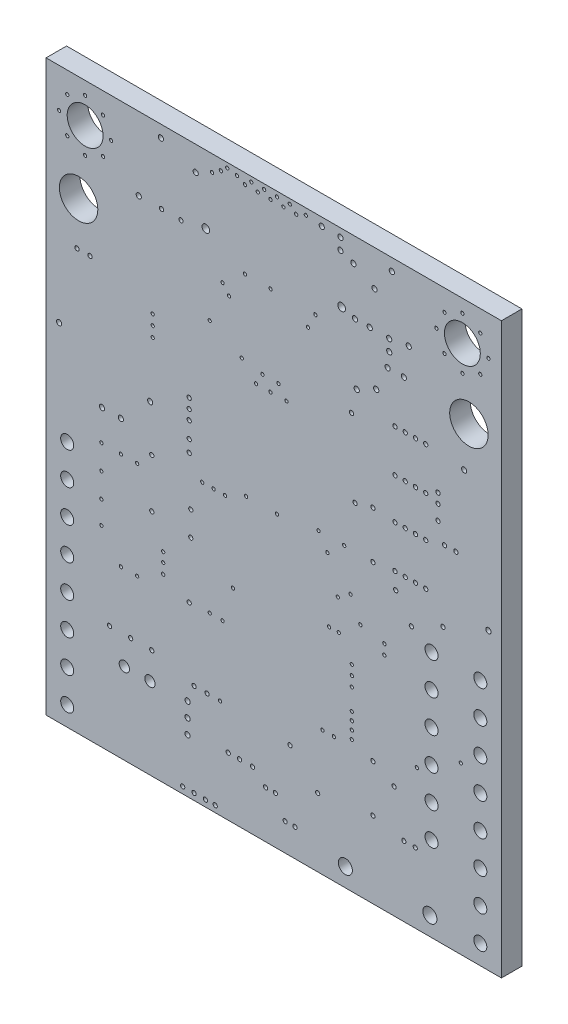
SolidWorks part; units mm, degrees
ref_plane "Спереди" through (0, 0, 0) normal (0, 0, 1) x (1, 0, 0)
ref_plane "Сверху" through (0, 0, 0) normal (0, 1, 0) x (1, 0, 0)
ref_plane "Справа" through (0, 0, 0) normal (1, 0, 0) x (0, 0, -1)
ref_plane "Dielectric_Layer Layer 1" through (0, 0, 1.6) normal (0, 0, 1) x (1, 0, 0)
sketch "Sketch1" plane through (0, 0, 0) normal (0, 0, 1) x (1, 0, 0)
  line L0 (0, 44.45) -> (0, 0)
  line L1 (0, 0) -> (35.56, 0)
  line L2 (35.56, 0) -> (35.56, 44.45)
  line L3 (35.56, 44.45) -> (0, 44.45)
extrude "Board_Outline" add sketch "Sketch1" along normal blind 1.6 separate body
sketch "Sketch2" plane through (0, 0, 0) normal (0, 0, 1) x (1, 0, 0)
  circle A0 centre (23.08, 39.14) radius 0.3
  circle A1 centre (12.48, 39.14) radius 0.3
  circle A2 centre (32.385, 12.954) radius 0.127
  circle A3 centre (15.621, 22.606) radius 0.127
  circle A4 centre (28.848, 23.368) radius 0.1651
  circle A5 centre (13.589, 7.747) radius 0.127
  circle A6 centre (19.53, 43.6372) radius 0.127
  circle A7 centre (24.543, 18.383) radius 0.127
  circle A8 centre (16.395, 30.607) radius 0.127
  circle A9 centre (22.098, 17.018) radius 0.127
  circle A10 centre (16.895, 31.496) radius 0.127
  circle A11 centre (22.86, 17.018) radius 0.127
  circle A12 centre (12.78, 33.067) radius 0.127
  circle A13 centre (15.53, 43.6372) radius 0.127
  circle A14 centre (12.192, 21.844) radius 0.127
  circle A15 centre (16.03, 44.069) radius 0.127
  circle A16 centre (13.081, 21.844) radius 0.127
  circle A17 centre (16.53, 43.6372) radius 0.127
  circle A18 centre (13.97, 21.844) radius 0.127
  circle A19 centre (17.03, 44.069) radius 0.127
  circle A20 centre (18.149, 31.496) radius 0.127
  circle A21 centre (18.03, 44.069) radius 0.127
  circle A22 centre (12.78, 13.288) radius 0.127
  circle A23 centre (19.03, 44.069) radius 0.127
  circle A24 centre (13.78, 13.272) radius 0.127
  circle A25 centre (17.526, 30.607) radius 0.127
  circle A26 centre (18.034, 22.606) radius 0.127
  circle A27 centre (18.776, 30.627) radius 0.127
  circle A28 centre (22.781, 19.383) radius 0.127
  circle A29 centre (15.28, 31.79) radius 0.127
  circle A30 centre (18.53, 43.6372) radius 0.127
  circle A31 centre (4.318, 20.574) radius 0.127
  circle A32 centre (4.318, 16.764) radius 0.127
  circle A33 centre (8.255, 21.717) radius 0.1651
  circle A34 centre (5.842, 20.574) radius 0.127
  circle A35 centre (7.112, 12.954) radius 0.127
  circle A36 centre (30.988, 21.463) radius 0.1651
  circle A37 centre (27.305, 22.098) radius 0.1651
  circle A38 centre (4.318, 18.669) radius 0.127
  circle A39 centre (4.318, 14.986) radius 0.127
  circle A40 centre (30.607, 30.353) radius 0.1651
  circle A41 centre (28.829, 5.461) radius 0.1651
  circle A42 centre (27.94, 5.461) radius 0.1651
  circle A43 centre (5.842, 12.954) radius 0.127
  circle A44 centre (11.303, 17.653) radius 0.1651
  circle A45 centre (7.112, 20.574) radius 0.127
  circle A46 centre (11.176, 26.289) radius 0.1651
  circle A47 centre (11.176, 27.051) radius 0.1651
  circle A48 centre (6.604, 8.509) radius 0.1651
  circle A49 centre (8.255, 8.509) radius 0.1651
  circle A50 centre (19.05, 7.493) radius 0.1651
  circle A51 centre (1.016, 27.051) radius 0.2032
  circle A52 centre (4.3688, 22.987) radius 0.2032
  circle A53 centre (25.527, 26.797) radius 0.1651
  circle A54 centre (25.527, 5.969) radius 0.1651
  circle A55 centre (30.607, 29.591) radius 0.1651
  circle A56 centre (11.176, 13.208) radius 0.1651
  circle A57 centre (11.176, 25.527) radius 0.1651
  circle A58 centre (15.113, 4.572) radius 0.1651
  circle A59 centre (14.224, 4.572) radius 0.1651
  circle A60 centre (16.129, 4.572) radius 0.1651
  circle A61 centre (11.557, 7.747) radius 0.1651
  circle A62 centre (24.13, 26.416) radius 0.1651
  circle A63 centre (34.544, 22.987) radius 0.2032
  circle A64 centre (28.525, 20.27) radius 0.1651
  circle A65 centre (28.848, 26.67) radius 0.1651
  circle A66 centre (32.648, 32.902) radius 0.2032
  circle A67 centre (23.85, 32.359) radius 0.1651
  circle A68 centre (17.907, 3.683) radius 0.1651
  circle A69 centre (17.145, 3.683) radius 0.1651
  circle A70 centre (11.049, 5.334) radius 0.2032
  circle A71 centre (25.781, 34.925) radius 0.2032
  circle A72 centre (27.94, 36.83) radius 0.2032
  circle A73 centre (26.67, 36.83) radius 0.2032
  circle A74 centre (25.654, 41.656) radius 0.2032
  circle A75 centre (24.257, 34.163) radius 0.2032
  circle A76 centre (17.53, 37.592) radius 0.127
  circle A77 centre (15.53, 37.592) radius 0.127
  circle A78 centre (21.03, 37.592) radius 0.127
  circle A79 centre (11.049, 4.191) radius 0.2032
  circle A80 centre (11.049, 6.477) radius 0.2032
  circle A81 centre (14.28, 35.489) radius 0.127
  circle A82 centre (14.149, 44.069) radius 0.127
  circle A83 centre (13.78, 36.132) radius 0.127
  circle A84 centre (13.649, 43.6372) radius 0.127
  circle A85 centre (21.59, 9.779) radius 0.127
  circle A86 centre (22.479, 9.779) radius 0.127
  circle A87 centre (9.144, 14.097) radius 0.127
  circle A88 centre (8.325, 29.699) radius 0.127
  circle A89 centre (8.325, 30.499) radius 0.127
  circle A90 centre (9.144, 14.883) radius 0.127
  circle A91 centre (9.144, 15.621) radius 0.127
  circle A92 centre (8.325, 31.299) radius 0.127
  circle A93 centre (3.048, 43.434) radius 0.127
  circle A94 centre (5.08, 41.402) radius 0.127
  circle A95 centre (5.842, 22.987) radius 0.2032
  circle A96 centre (7.239, 38.735) radius 0.2032
  circle A97 centre (1.016, 41.402) radius 0.127
  circle A98 centre (3.048, 39.37) radius 0.127
  circle A99 centre (8.966, 43.51) radius 0.2032
  circle A100 centre (27, 43.51) radius 0.2032
  circle A101 centre (24.003, 42.545) radius 0.2032
  circle A102 centre (11.684, 42.545) radius 0.2032
  circle A103 centre (4.445, 42.799) radius 0.127
  circle A104 centre (1.651, 42.799) radius 0.127
  circle A105 centre (1.651, 40.005) radius 0.127
  circle A106 centre (4.445, 40.005) radius 0.127
  circle A107 centre (32.512, 43.434) radius 0.127
  circle A108 centre (30.48, 41.402) radius 0.127
  circle A109 centre (34.544, 41.402) radius 0.127
  circle A110 centre (32.512, 39.37) radius 0.127
  circle A111 centre (31.115, 42.799) radius 0.127
  circle A112 centre (31.115, 40.005) radius 0.127
  circle A113 centre (33.909, 42.799) radius 0.127
  circle A114 centre (33.909, 40.005) radius 0.127
  circle A115 centre (29.648, 23.368) radius 0.1651
  circle A116 centre (14.597, 15.883) radius 0.127
  circle A117 centre (30.607, 28.448) radius 0.1651
  circle A118 centre (29.648, 29.845) radius 0.1651
  circle A119 centre (26.416, 17.272) radius 0.127
  circle A120 centre (28.848, 29.845) radius 0.1651
  circle A121 centre (26.416, 18.034) radius 0.127
  circle A122 centre (28.048, 29.845) radius 0.1651
  circle A123 centre (27.248, 26.67) radius 0.1651
  circle A124 centre (28.048, 26.67) radius 0.1651
  circle A125 centre (27.248, 29.845) radius 0.1651
  circle A126 centre (21.28, 23.114) radius 0.127
  circle A127 centre (23.876, 11.557) radius 0.127
  circle A128 centre (23.876, 12.192) radius 0.127
  circle A129 centre (23.876, 10.287) radius 0.127
  circle A130 centre (23.876, 10.922) radius 0.127
  circle A131 centre (21.971, 21.971) radius 0.127
  circle A132 centre (23.28, 23.114) radius 0.127
  circle A133 centre (20.447, 36.449) radius 0.127
  circle A134 centre (23.78, 20.066) radius 0.127
  circle A135 centre (23.876, 13.843) radius 0.127
  circle A136 centre (23.876, 14.605) radius 0.127
  circle A137 centre (28.956, 10.922) radius 0.127
  circle A138 centre (23.876, 15.367) radius 0.127
  circle A139 centre (21.209, 5.334) radius 0.1651
  circle A140 centre (27.178, 8.763) radius 0.1651
  circle A141 centre (11.303, 19.558) radius 0.1651
  circle A142 centre (25.527, 23.114) radius 0.1651
  circle A143 centre (11.176, 24.257) radius 0.1651
  circle A144 centre (8.255, 17.907) radius 0.1651
  circle A145 centre (3.429, 32.766) radius 0.1651
  circle A146 centre (11.176, 23.33) radius 0.1651
  circle A147 centre (4.953, 8.509) radius 0.1651
  circle A148 centre (25.527, 9.652) radius 0.1651
  circle A149 centre (2.413, 32.766) radius 0.1651
  circle A150 centre (28.321, 39.116) radius 0.2032
  circle A151 centre (8.128, 25.273) radius 0.2032
  circle A152 centre (12.573, 7.747) radius 0.1651
  circle A153 centre (28.048, 23.368) radius 0.1651
  circle A154 centre (27.248, 23.368) radius 0.1651
  circle A155 centre (29.648, 26.67) radius 0.1651
  circle A156 centre (27.248, 33.147) radius 0.1651
  circle A157 centre (29.648, 33.147) radius 0.1651
  circle A158 centre (28.048, 33.147) radius 0.1651
  circle A159 centre (28.848, 33.147) radius 0.1651
  circle A160 centre (25.273, 38.862) radius 0.2032
  circle A161 centre (24.13, 38.862) radius 0.2032
  circle A162 centre (22.987, 43.815) radius 0.2032
  circle A163 centre (22.987, 42.926) radius 0.2032
  circle A164 centre (31.115, 27.051) radius 0.1651
  circle A165 centre (32.004, 27.051) radius 0.1651
  circle A166 centre (12.954, 43.18) radius 0.127
  circle A167 centre (14.903, 43.942) radius 0.127
  circle A168 centre (17.53, 43.6372) radius 0.127
  circle A169 centre (20.284, 43.942) radius 0.127
  circle A170 centre (9.017, 38.735) radius 0.1651
  circle A171 centre (10.541, 38.735) radius 0.1651
  circle A172 centre (13.208, 0.508) radius 0.1651
  circle A173 centre (12.446, 0.508) radius 0.1651
  circle A174 centre (11.557, 0.508) radius 0.1651
  circle A175 centre (10.668, 0.508) radius 0.1651
  circle A176 centre (26.797, 37.973) radius 0.2032
  circle A177 centre (26.797, 38.862) radius 0.2032
  circle A178 centre (21.53, 43.8185) radius 0.2032
  circle A179 centre (18.669, 2.159) radius 0.1651
  circle A180 centre (19.431, 2.159) radius 0.1651
extrude "NPTH" cut sketch "Sketch2" along normal through all
sketch "Sketch3" plane through (0, 0, 0) normal (0, 0, 1) x (1, 0, 0)
  circle A0 centre (3.05, 41.4) radius 1.4
  circle A1 centre (32.51, 41.4) radius 1.4
  circle A2 centre (1.65, 19.3) radius 0.51
  circle A3 centre (1.65, 16.76) radius 0.51
  circle A4 centre (1.65, 14.22) radius 0.51
  circle A5 centre (1.65, 11.68) radius 0.51
  circle A6 centre (1.65, 9.14) radius 0.51
  circle A7 centre (1.65, 6.6) radius 0.51
  circle A8 centre (1.65, 4.06) radius 0.51
  circle A9 centre (1.65, 1.52) radius 0.51
  circle A10 centre (33.91, 19.3) radius 0.51
  circle A11 centre (33.91, 16.76) radius 0.51
  circle A12 centre (33.91, 14.22) radius 0.51
  circle A13 centre (33.91, 11.68) radius 0.51
  circle A14 centre (33.91, 9.14) radius 0.51
  circle A15 centre (33.91, 6.6) radius 0.51
  circle A16 centre (33.91, 4.06) radius 0.51
  circle A17 centre (33.91, 1.52) radius 0.51
  circle A18 centre (30.1, 19.3) radius 0.51
  circle A19 centre (30.1, 16.76) radius 0.51
  circle A20 centre (30.1, 14.22) radius 0.51
  circle A21 centre (30.1, 11.68) radius 0.51
  circle A22 centre (30.1, 9.14) radius 0.51
  circle A23 centre (30.1, 6.6) radius 0.51
  circle A24 centre (2.54, 36.2) radius 1.5
  circle A25 centre (33.02, 36.2) radius 1.5
  circle A26 centre (23.37, 1.45) radius 0.55
  circle A27 centre (29.97, 1.45) radius 0.55
  circle A28 centre (6.11, 6.35) radius 0.4
  circle A29 centre (8.11, 6.35) radius 0.4
extrude "PTH" cut sketch "Sketch3" along normal through all
